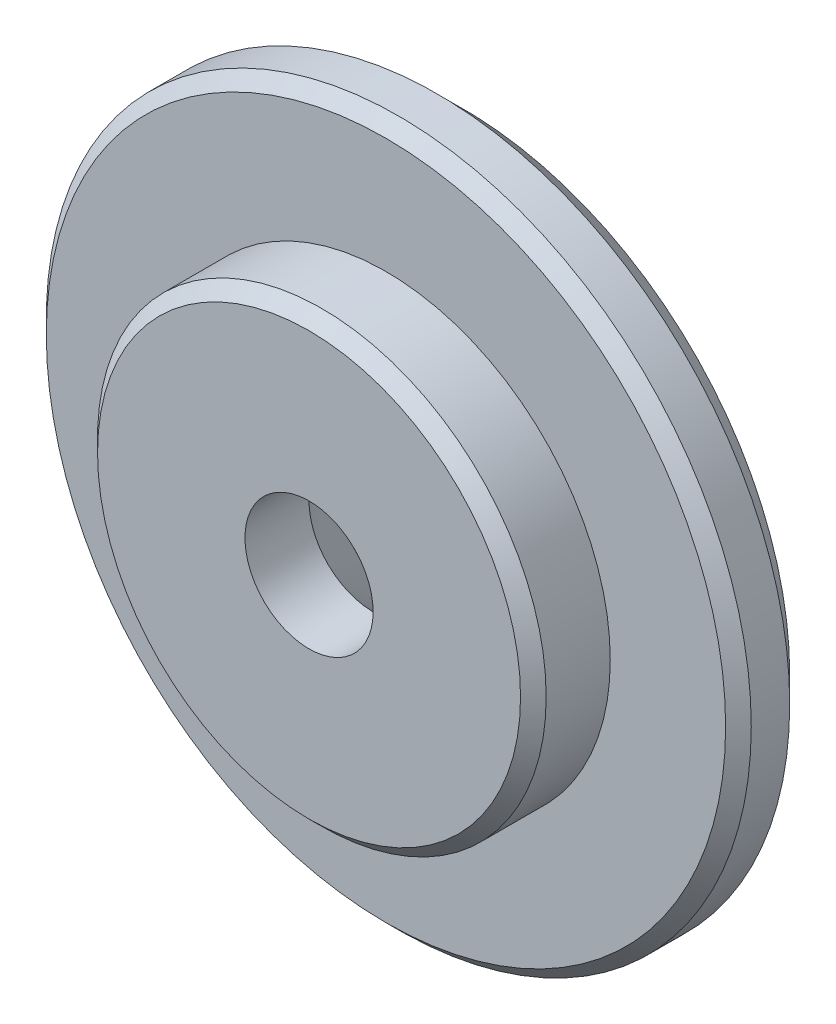
SolidWorks part; units mm, degrees
ref_plane "Alzado" through (0, 0, 0) normal (0, 0, 1) x (1, 0, 0)
ref_plane "Planta" through (0, 0, 0) normal (0, 1, 0) x (1, 0, 0)
ref_plane "Vista lateral" through (0, 0, 0) normal (1, 0, 0) x (0, 0, -1)
sketch "Croquis1" plane through (0, 0, 0) normal (0, 1, 0) x (1, 0, 0)
  line L0 (17.5121, -5.97) -> (27.5121, -5.97)
  line L2 (27.5121, -5.97) -> (27.5121, 0.03)
  line L4 (27.5121, 0.03) -> (12.0121, 0.03)
  line L5 (12.0121, 0.03) -> (5.0121, -6.97)
  line L6 (5.0121, -6.97) -> (5.0121, -11.97)
  line L7 (5.0121, -11.97) -> (17.5121, -11.97)
  line L9 (17.5121, -11.97) -> (17.5121, -5.97)
  line L10 (0.0121, 0) -> (0.0121, -11.97) construction
  dimension "D1" = 12
  dimension "D2" = 6
  dimension "D3" = 5
  dimension "D4" = 35
  dimension "D5" = 55
  dimension "D6" = 10
  dimension "D7" = 45
revolve "Revolución1" add sketch "Croquis1" angle 360 about L10
chamfer "Chaflán1" distance 2 angle 45 1 edges at (27.5121, 0, -0.03)
chamfer "Chaflán2" distance 1 angle 45 2 edges at (17.5121, 0, 11.97) (27.5121, 0, 5.97)
